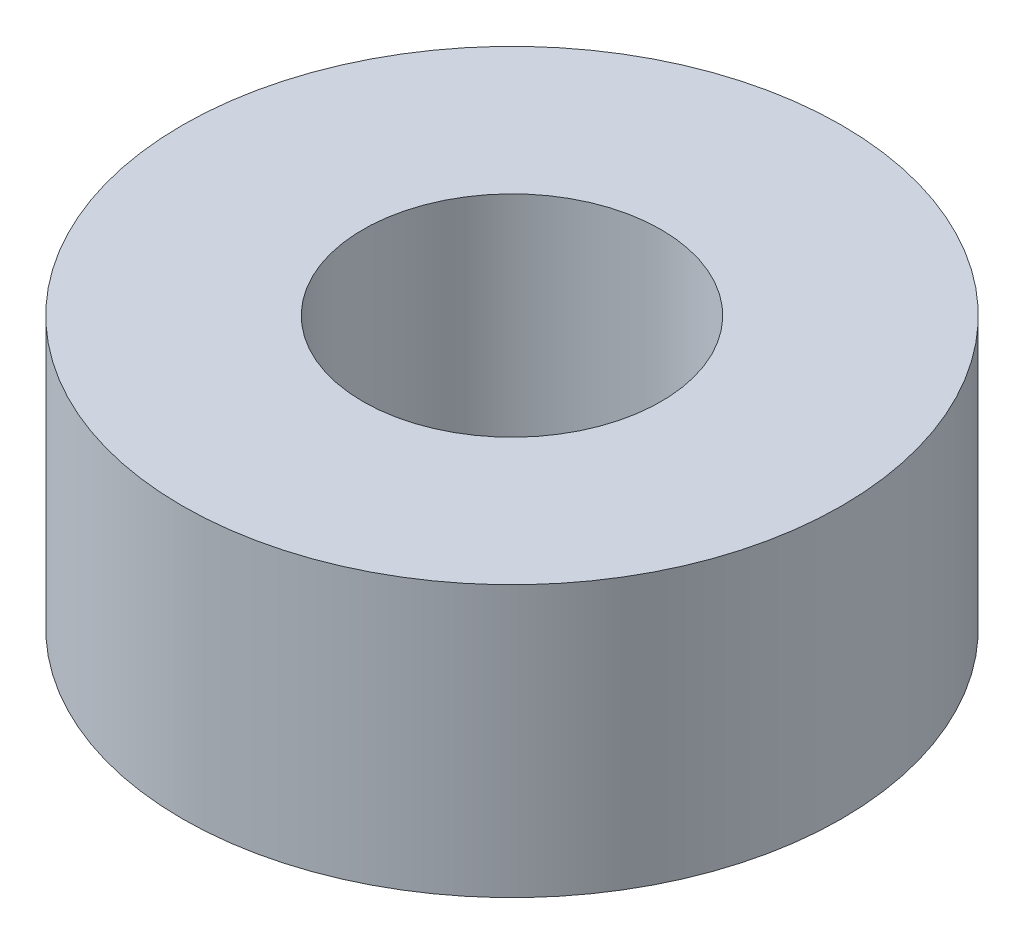
SolidWorks part; units mm, degrees
ref_plane "前视基准面" through (0, 0, 0) normal (0, 0, 1) x (1, 0, 0)
ref_plane "上视基准面" through (0, 0, 0) normal (0, 1, 0) x (1, 0, 0)
ref_plane "右视基准面" through (0, 0, 0) normal (1, 0, 0) x (0, 0, -1)
sketch "草图1" plane through (0, 0, 0) normal (0, 1, 0) x (1, 0, 0)
  circle A0 centre (0, 0) radius 1.65
  circle A1 centre (0, 0) radius 3.65
  dimension "D1" = 2
extrude "凸台-拉伸1" add sketch "草图1" along normal blind 3
